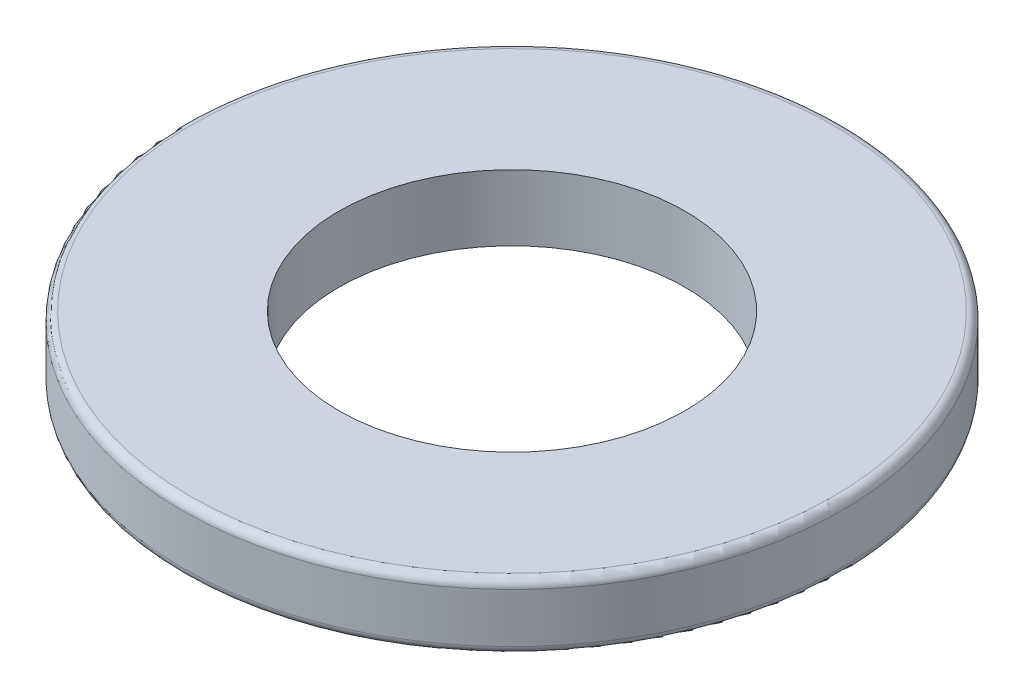
SolidWorks part; units mm, degrees
material "Stal nierdzewna (ferrytyczna)"
ref_plane "Płaszczyzna XY" through (0, 0, 0) normal (0, 0, 1) x (1, 0, 0)
ref_plane "Płaszczyzna XZ" through (0, 0, 0) normal (0, 1, 0) x (1, 0, 0)
ref_plane "Płaszczyzna YZ" through (0, 0, 0) normal (1, 0, 0) x (0, 0, -1)
sketch "Szkic1" plane through (0, 0, 0) normal (0, 1, 0) x (1, 0, 0)
  circle A0 centre (0, 17.0025) radius 8
  circle A1 centre (0, 17.0025) radius 4.2
  dimension "D1" = 16
  dimension "D2" = 8.4
extrude "Dodanie-wyciągnięcie1" add sketch "Szkic1" along normal blind 1.6
fillet "Zaokrąglenie1" radius 0.2 2 edges at (0, 0, -9.0025) (0, 1.6, -9.0025)
